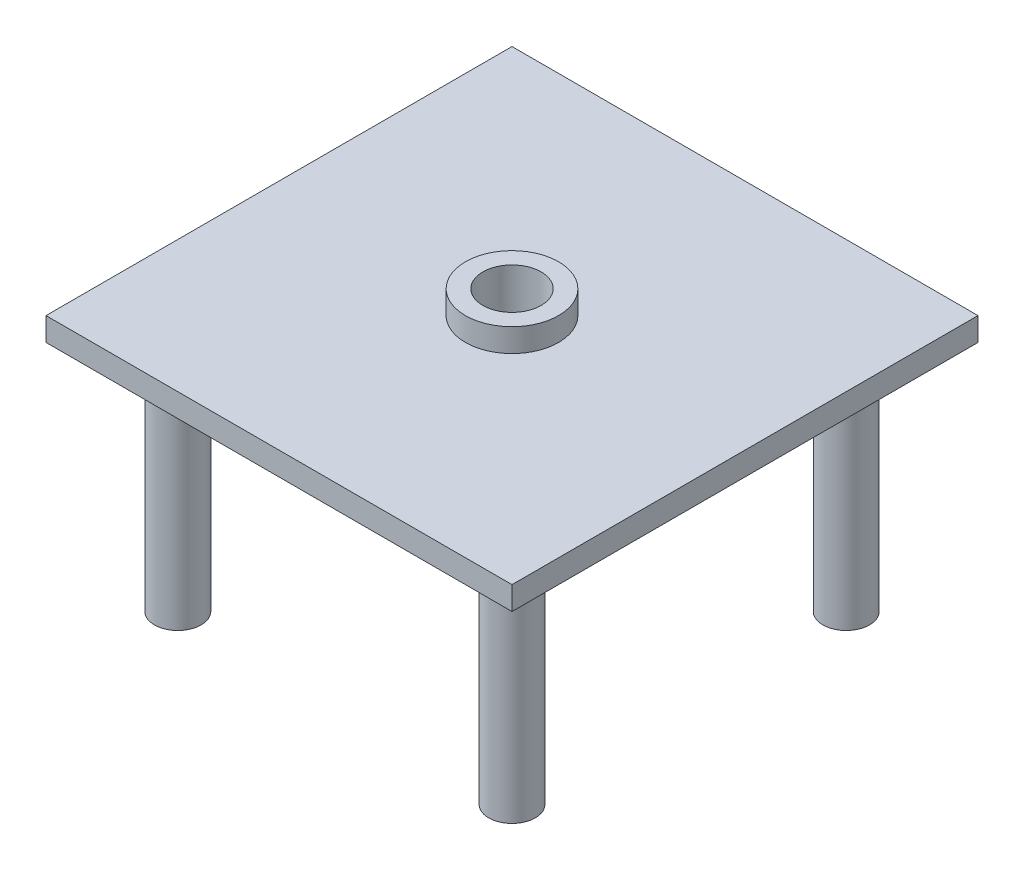
SolidWorks part; units mm, degrees
ref_plane "Front Plane" through (0, 0, 0) normal (0, 0, 1) x (1, 0, 0)
ref_plane "Top Plane" through (0, 0, 0) normal (0, 1, 0) x (1, 0, 0)
ref_plane "Right Plane" through (0, 0, 0) normal (1, 0, 0) x (0, 0, -1)
sketch "Sketch1" plane through (0, 0, 0) normal (0, 1, 0) x (1, 0, 0)
  line L5 (-200, -200) -> (200, 200) construction
  line L6 (-200, 200) -> (200, -200) construction
  circle A0 centre (-143.4315, 143.4315) radius 20
  circle A1 centre (-143.4315, -143.4315) radius 20
  circle A2 centre (143.4315, -143.4315) radius 20
  circle A3 centre (143.4315, 143.4315) radius 20
  point P0 (0, 0)
  point P17 (0, 0)
  dimension "D3" = 4
  dimension "D5" = 40
  dimension "D1" = 400
  dimension "D2" = 400
  dimension "D4" = 80
extrude "Boss-Extrude1" add sketch "Sketch1" along normal blind 200
sketch "Sketch2" plane through (0, 200, 0) normal (0, 1, 0) x (1, 0, 0)
  line L1 (-200, 200) -> (200, 200)
  line L2 (-200, 200) -> (-200, -200)
  line L3 (-200, -200) -> (200, -200)
  line L4 (200, 200) -> (200, -200)
  line L5 (-200, 200) -> (200, -200) construction
  line L6 (-200, -200) -> (200, 200) construction
  circle A0 centre (0, 0) radius 25
  point P0 (0, 0)
  dimension "D1" = 400
  dimension "D3" = 50
  dimension "D2" = 400
extrude "Boss-Extrude2" add sketch "Sketch2" along normal blind 20
sketch "Sketch3" plane through (0, 220, 0) normal (0, 1, 0) x (1, 0, 0)
  circle A0 centre (0, 0) radius 25
  circle A1 centre (0, 0) radius 40
extrude "Boss-Extrude3" add sketch "Sketch3" along normal blind 20
